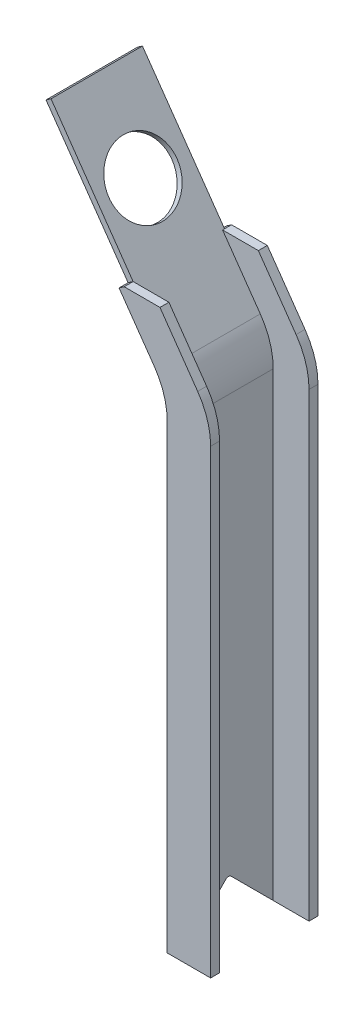
SolidWorks part; units mm, degrees
material "Plain Carbon Steel"
ref_plane "Front Plane" through (0, 0, 0) normal (0, 0, 1) x (1, 0, 0)
ref_plane "Top Plane" through (0, 0, 0) normal (0, 1, 0) x (1, 0, 0)
ref_plane "Right Plane" through (0, 0, 0) normal (1, 0, 0) x (0, 0, -1)
sketch "Sketch1" plane through (0, 0, 0) normal (0, 0, 1) x (1, 0, 0)
  line L0 (0, 0) -> (0, 342.9)
  line L1 (0, 342.9) -> (-34.1864, 391.7232)
  line L3 (-23.7317, 384.5129) -> (5.406, 342.9)
  line L4 (5.406, 342.9) -> (5.406, 0)
  line L5 (5.406, 0) -> (0, 0)
  line L8 (-34.1864, 391.7232) -> (-25.5837, 397.7469) construction
  line L11 (-51.3182, 423.9106) -> (-58.5014, 434.1692) construction
  line L12 (-34.1864, 391.7232) -> (-30.5589, 394.2632)
  line L13 (-30.5589, 394.2632) -> (-23.7317, 384.5129)
  dimension "D1" = 342.9
  dimension "D2" = 50.8
  dimension "D3" = 12.7
  dimension "D4" = 145
  dimension "D5" = 59.6022
  dimension "D7" = 90
extrude "Boss-Extrude1" add sketch "Sketch1" along normal blind 76.2
sketch "Sketch9" plane through (0, 0, 0) normal (0, 0, 1) x (1, 0, 0)
  line L8 (5.406, 0) -> (30.806, 0)
  line L9 (30.806, 0) -> (30.806, 342.9)
  line L10 (30.806, 342.9) -> (-5.1589, 394.2632)
  line L11 (-5.1589, 394.2632) -> (-30.5589, 394.2632)
  line L12 (-30.5589, 394.2632) -> (5.406, 342.9)
  line L13 (5.406, 342.9) -> (5.406, 0)
  dimension "D1" = 342.9
  dimension "D3" = 25.4
  dimension "D4" = 25.4
extrude "Boss-Extrude8" add sketch "Sketch9" along normal blind 6.35
pattern_linear "LPattern3" count 2 spacing 69.85 along (0, 0, 1) of "Boss-Extrude8"
fillet "Fillet2" radius 50.8 4 edges at (0, 342.9, 38.1) (30.806, 342.9, 3.175) (5.406, 342.9, 38.1) (30.806, 342.9, 73.025)
sketch "Sketch12" plane through (164.7378, 115.3506, 0) normal (0.8192, 0.5736, 0) x (0, 0, -1)
  line L2 (-69.85, 340.4894) -> (-4.9549, 340.4894)
  line L3 (-69.85, 340.4894) -> (-69.85, 442.0894)
  line L4 (-69.85, 442.0894) -> (-4.9549, 442.0894)
  line L5 (-4.9549, 340.4894) -> (-4.9549, 442.0894)
  dimension "D1" = 101.6
extrude "Boss-Extrude10" add sketch "Sketch12" against normal blind 4.318
sketch "Sketch10" plane through (164.7378, 115.3506, 0) normal (0.8192, 0.5736, 0) x (0, 0, -1)
  line L0 (-38.1, 384.7749) -> (-38.1, 323.6608) construction
  line L2 (-4.9549, 442.0894) -> (-69.85, 442.0894) construction
  line L3 (-69.85, 442.0894) -> (-69.85, 340.4894) construction
  circle A0 centre (-38.1, 383.6694) radius 24.13
  dimension "D1" = 48.26
  dimension "D2" = 58.42
  dimension "D3" = 31.75
extrude "Top Circle Cut" cut sketch "Sketch10" against normal up to next
sketch "Sketch13" plane through (5.406, 0, 0) normal (1, 0, 0) x (0, 0, -1)
  line L2 (-38.1, 31.75) -> (-69.85, 0)
  line L3 (-69.85, 0) -> (-6.35, 0)
  line L4 (-6.35, 0) -> (-38.1, 31.75)
  dimension "D2" = 44.9013
  dimension "D3" = 44.9013
extrude "Cut-Extrude2" cut sketch "Sketch13" against normal through all both and the other way through all
fillet "Fillet3" radius 2.54 1 edges at (2.703, 31.75, 38.1)
